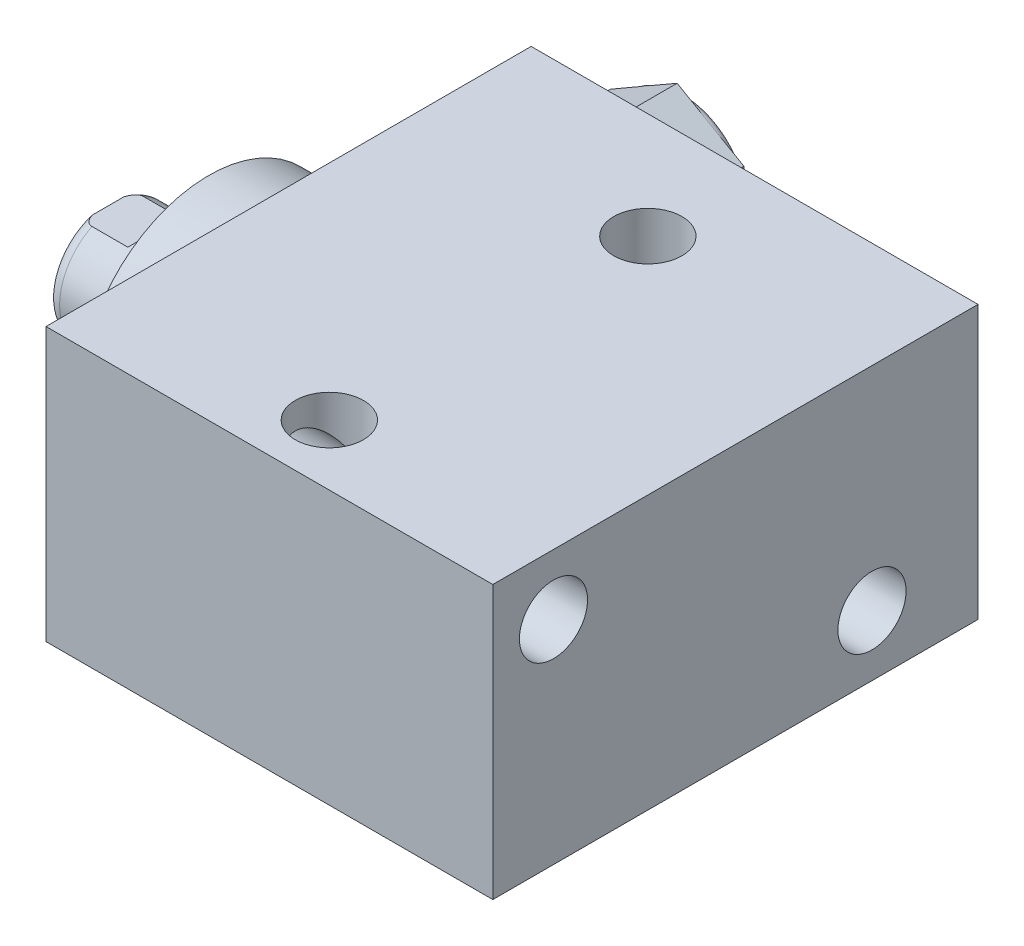
SolidWorks part; units mm, degrees
material "Alloy Steel"
ref_plane "Front Plane" through (0, 0, 0) normal (0, 0, 1) x (1, 0, 0)
ref_plane "Top Plane" through (0, 0, 0) normal (0, 1, 0) x (1, 0, 0)
ref_plane "Right Plane" through (0, 0, 0) normal (1, 0, 0) x (0, 0, -1)
ref_plane "Plane1" through (0, 0, 0) normal (1, 0, 0) x (0, 0, -1)
sketch "Sketch1" plane through (0, 0, 0) normal (1, 0, 0) x (0, 0, -1)
  line L0 (-23.0124, 14.2875) -> (27.7876, 14.2875)
  line L1 (27.7876, 14.2875) -> (27.7876, -14.2875)
  line L2 (27.7876, -14.2875) -> (-23.0124, -14.2875)
  line L3 (-23.0124, -14.2875) -> (-23.0124, 14.2875)
  line L4 (0, -24.4475) -> (0, 24.4475) construction
  dimension "D1" = 28.575
  dimension "D2" = 14.2875
  dimension "D3" = 50.8
  dimension "D4" = 23.0124
extrude "Extrude1" add sketch "Sketch1" along normal blind 46.7868
ref_plane "Plane12" through (0, 4.7625, 0) normal (0, 1, 0) x (-1, 0, 0)
sketch "S2D0002" plane through (0, 4.7625, 0) normal (0, 1, 0) x (-1, 0, 0)
  line L0 (-14.5415, -27.5336) -> (-18.161, -27.5336)
  line L1 (-14.5415, -27.5082) -> (-14.5415, -27.5336)
  line L2 (-14.5415, -27.5082) -> (-13.9446, -26.9113)
  line L3 (-13.9446, -26.9113) -> (-13.9446, -14.0716)
  line L4 (-13.9446, -14.0716) -> (-9.525, -14.0716)
  line L5 (-9.525, -14.0716) -> (-9.525, -27.7876)
  line L6 (-9.525, -19.1384) -> (-9.525, 0.6985) construction
  line L7 (0, -27.7876) -> (0, 23.0124) construction
  line L8 (-18.161, -27.7876) -> (-18.161, -27.5336)
  line L9 (-46.7868, -27.7876) -> (0, -27.7876) construction
  line L10 (-18.161, -27.7876) -> (-9.525, -27.7876)
  dimension "D1" = 13.716
  dimension "D2" = 9.525
  dimension "D3" = 8.8392
  dimension "D4" = 45
  dimension "D5" = 0.6223
  dimension "D6" = 10.033
  dimension "D7" = 0.0254
  dimension "D8" = 0.254
  dimension "D9" = 17.272
revolve "Cut-Revolve1" cut sketch "S2D0002" angle 360 about L6
pattern_linear "LPattern1" count 2 spacing 27.94 along (1, 0, 0) of "Cut-Revolve1"
sketch "Sketch5" plane through (0, 0, 0) normal (-1, 0, 0) x (0, 0, 1)
  circle A0 centre (0, 0) radius 13.5001
  dimension "D1" = 27.0002
extrude "Extrude2" add sketch "Sketch5" along normal blind 5.969
ref_plane "Plane5" through (0, 0, 0) normal (0, -1, 0) x (0, 0, 1)
sketch "Sketch6" plane through (0, 0, 0) normal (0, -1, 0) x (0, 0, 1)
  line L0 (0, 5.969) -> (-6.3373, 5.969)
  line L1 (-6.3373, 5.969) -> (-6.3373, 16.51)
  line L2 (-6.3373, 16.51) -> (0, 16.51)
  line L3 (0, 16.51) -> (0, 5.969)
  line L4 (0, -5.7546) -> (0, 21.1709) construction
  line L5 (13.5001, 5.969) -> (-13.5001, 5.969) construction
  line L6 (23.0124, -46.7868) -> (-27.7876, -46.7868) construction
  dimension "D1" = 63.2968
  dimension "D2" = 12.6746
revolve "Revolve1" add sketch "Sketch6" angle 360 about L4
ref_plane "Plane6" through (-18.5113, 3.2639, 0) normal (0, 0, 1) x (0, 1, 0)
sketch "S2D0001" plane through (-18.5113, 3.2639, 0) normal (0, 0, 1) x (0, 1, 0)
  line L0 (-0.7493, -3.3651) -> (-0.7493, -18.0033)
  line L1 (-3.2639, -19.5142) -> (-0.7493, -18.0033)
  line L2 (0.0381, -2.0013) -> (-3.2639, -2.0013)
  line L3 (-3.2639, -2.0013) -> (-3.2639, -19.5142)
  line L4 (-0.7493, -3.3651) -> (0.0381, -2.0013)
  line L5 (-3.2639, -18.5113) -> (-3.2639, 2.765) construction
  line L6 (3.0734, -2.0013) -> (-9.6012, -2.0013) construction
  dimension "D1" = 30
  dimension "D2" = 6.604
  dimension "D3" = 5.0292
  dimension "D4" = 16.002
  dimension "D5" = 59
revolve "Cut-Revolve4" cut sketch "S2D0001" angle 360 about L5
ref_plane "Plane7" through (0, 0, 0) normal (0, 1, 0) x (0, 0, -1)
sketch "Sketch8" plane through (0, 0, 0) normal (0, 1, 0) x (0, 0, -1)
  line L0 (-6.3373, 10.1854) -> (-6.096, 10.9474)
  line L1 (-6.096, 10.9474) -> (-6.096, 15.494)
  line L2 (0, 12.6594) -> (0, 20.8178) construction
  line L3 (-6.3373, 10.1854) -> (-6.3373, 16.51)
  line L4 (-5.7079, 16.51) -> (-6.3373, 16.51)
  line L5 (6.3373, 16.51) -> (-6.3373, 16.51) construction
  line L6 (-6.3373, 16.51) -> (-6.3373, 5.969) construction
  arc A0 (-5.7079, 16.51) -> (-6.096, 15.494) centre (-4.572, 15.494) ccw
  dimension "D2" = 1.524
  dimension "D1" = 12.192
  dimension "D3" = 1.016
  dimension "D4" = 0.762
  dimension "D5" = 5.5626
revolve "Cut-Revolve5" cut sketch "Sketch8" angle 360 about L2
ref_plane "Plane11" through (0, 0, 0) normal (0, 0, -1) x (0, -1, 0)
sketch "Sketch12" plane through (0, 0, 0) normal (0, 0, -1) x (0, -1, 0)
  line L0 (5.461, 16.51) -> (5.461, 11.7348)
  line L1 (5.461, 11.7348) -> (6.096, 11.0998)
  line L2 (-5.461, 16.51) -> (-5.461, 11.7348)
  line L3 (-5.461, 11.7348) -> (-6.096, 11.0998)
  line L4 (5.461, 16.51) -> (6.096, 16.51)
  line L5 (0, 13.7262) -> (0, 20.767) construction
  line L6 (-6.096, 11.0998) -> (-6.096, 16.51)
  line L8 (6.096, 10.9474) -> (6.096, 15.494) construction
  line L9 (6.096, 11.0998) -> (6.096, 16.51)
  line L10 (-5.461, 16.51) -> (-6.096, 16.51)
  line L12 (5.7079, 16.51) -> (-5.7079, 16.51) construction
  dimension "D1" = 10.922
  dimension "D2" = 4.7752
  dimension "D3" = 45
extrude "Cut-Extrude4" cut sketch "Sketch12" against normal mid plane 60.96
hole_wizard "Hole1" positions "Sketch15" profile "Sketch14" legacy end condition up to next
sketch "Sketch15" plane through (0, 0, 0) normal (-1, 0, 0) x (0, 0, 1)
  line L0 (0, 0) -> (-29.9914, 0) construction
  line L1 (0, 0) -> (0, 25.7648) construction
  point P0 (-16.6878, -7.9248)
  point P11 (16.6624, 7.9502)
  dimension "D1" = 7.9248
  dimension "D2" = 16.6878
  dimension "D3" = 15.875
  dimension "D4" = 33.3502
sketch "Sketch14" plane through (0, -7.9248, -16.6878) normal (0, 1, 0) x (0, 0, 1)
  line L0 (0, 0) -> (0, 46.7868)
  line L1 (0, 46.7868) -> (3.5685, 46.7868)
  line L2 (3.5685, 46.7868) -> (3.5685, 0)
  line L3 (3.5685, 0) -> (0, 0)
  line L4 (0, 110) -> (0, -10) construction
  dimension "Diameter" = 7.137
  dimension "Depth" = 46.7868
hole_wizard "Hole2" positions "Sketch17" profile "Sketch16" legacy
sketch "Sketch17" plane through (0, 14.2875, 0) normal (0, 1, 0) x (-1, 0, 0)
  line L0 (0, 0) -> (-59.3363, 0) construction
  line L1 (0, -27.7876) -> (0, 23.0124) construction
  point P0 (-23.3172, -16.6878)
  point P9 (-23.3172, 16.6624)
  dimension "D1" = 33.3502
  dimension "D2" = 23.3172
  dimension "D3" = 16.6878
sketch "Sketch16" plane through (23.3172, 14.2875, -16.6878) normal (1, 0, 0) x (0, 0, 1)
  line L0 (0, 0) -> (0, 28.575)
  line L1 (0, 28.575) -> (3.5685, 28.575)
  line L2 (3.5685, 28.575) -> (3.5685, 0)
  line L3 (3.5685, 0) -> (0, 0)
  line L4 (0, 110) -> (0, -10) construction
  dimension "Diameter" = 7.137
  dimension "Depth" = 28.575
sketch "Sketch18" plane through (0, 0, -27.5336) normal (0, 0, -1) x (-1, 0, 0)
  line L1 (-2.54, 8.7953) -> (-9.525, 12.8281)
  line L2 (-9.525, 12.8281) -> (-16.51, 8.7953)
  line L3 (-16.51, 8.7953) -> (-16.51, 0.7297)
  line L4 (-16.51, 0.7297) -> (-9.525, -3.3031)
  line L5 (-9.525, -3.3031) -> (-2.54, 0.7297)
  line L6 (-2.54, 0.7297) -> (-2.54, 8.7953)
  circle A0 centre (-9.525, 4.7625) radius 6.985 construction
  dimension "D1" = 13.97
extrude "Extrude3" add sketch "Sketch18" along normal blind 6.779
sketch "Sketch19" plane through (0, 4.7625, 0) normal (0, 1, 0) x (-1, 0, 0)
  line L0 (-9.525, -18.5103) -> (-9.525, -44.3941) construction
  line L1 (-9.525, -14.0716) -> (-9.525, -26.9113) construction
  line L2 (-9.525, -34.3126) -> (-16.51, -34.3126) construction
  line L3 (-16.51, -34.3126) -> (-16.51, -27.5336) construction
  line L4 (-15.748, -34.3126) -> (-15.748, -36.7256)
  line L5 (-15.748, -36.7256) -> (-18.923, -36.7256)
  line L6 (-18.923, -36.7256) -> (-18.923, -33.5506)
  line L7 (-18.923, -33.5506) -> (-16.51, -33.5506)
  arc A0 (-16.51, -33.5506) -> (-15.748, -34.3126) centre (-15.748, -33.5506) ccw
  dimension "D1" = 0.762
  dimension "D2" = 3.175
  dimension "D3" = 3.175
revolve "Cut-Revolve6" cut sketch "Sketch19" angle 360 about L0
